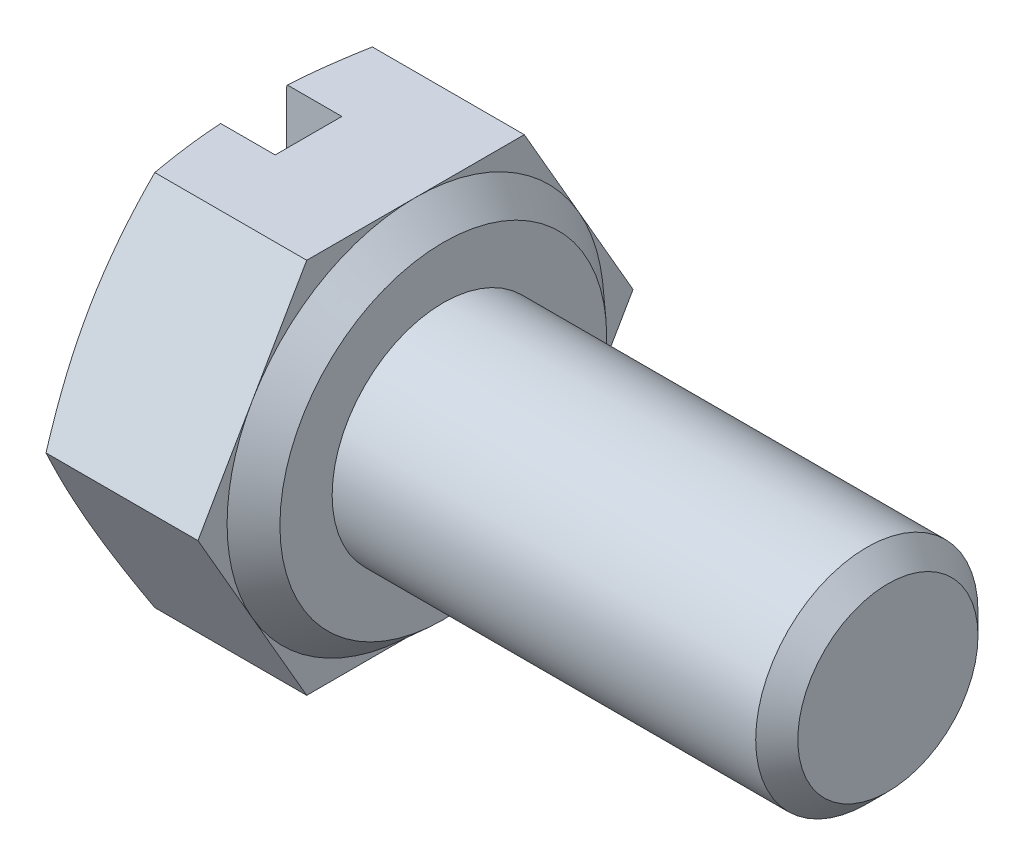
SolidWorks part; units mm, degrees
ref_plane "Front" through (0, 0, 0) normal (0, 0, 1) x (1, 0, 0)
ref_plane "Top" through (0, 0, 0) normal (0, 1, 0) x (1, 0, 0)
ref_plane "Right" through (0, 0, 0) normal (1, 0, 0) x (0, 0, -1)
sketch "Sketch-BaseHead" plane through (0, 0, 0) normal (1, 0, 0) x (0, 0, -1)
  line L1 (1.9572, -3.39) -> (3.9144, 0)
  line L2 (3.9144, 0) -> (1.9572, 3.39)
  line L3 (1.9572, 3.39) -> (-1.9572, 3.39)
  line L4 (-1.9572, 3.39) -> (-3.9144, 0)
  line L5 (-3.9144, 0) -> (-1.9572, -3.39)
  line L6 (-1.9572, -3.39) -> (1.9572, -3.39)
  circle A0 centre (0, 0) radius 3.39 construction
  dimension "s" = 6.78
extrude "BaseHead" add sketch "Sketch-BaseHead" along normal blind 2.925
ref_plane "Plane1" through (3.325, 0, 0) normal (1, 0, 0) x (0, 0, -1)
sketch "Sketch1" plane through (0, 0, 0) normal (0, 0, 1) x (1, 0, 0)
  line L0 (2.925, 0) -> (3.425, 0)
  line L1 (3.425, 0) -> (3.425, -2.94)
  line L2 (3.425, -2.94) -> (2.925, -3.39)
  line L3 (2.925, -3.39) -> (2.925, 0)
  dimension "D1" = 3.39
  dimension "D2" = 0.5
  dimension "D3" = 2.94
revolve "Revolve1" add sketch "Sketch1" angle 360 about axis through (-4.0016, 0, 0) along (1, 0, 0)
sketch "Sketch3" plane through (3.425, 0, 0) normal (1, 0, 0) x (0, 0, -1)
  circle A0 centre (0, 0) radius 2
  dimension "d" = 4
extrude "BaseBody" add sketch "Sketch3" along normal blind 8
cosmetic thread "ThreadCosmetic1" parameters "D2"=3.242
chamfer "Chamfer1" distance 0.379 angle 45 1 edges at (11.425, 0, -2)
fillet "HeadFillet" [suppressed] radius 0.2
sketch "Sketch4" plane through (-0.2646, 0, 5.9169) normal (0, 1, 0) x (0, 0, -1)
  line L0 (5.9169, 3.7369) -> (5.9169, -10.4477) construction
  line L2 (9.8313, -0.2646) -> (9.3069, -0.2646)
  line L4 (9.3069, -0.2646) -> (9.8313, -0.4555)
  line L6 (9.8313, -0.4555) -> (9.8313, -0.2646)
  dimension "D1" = 20
  dimension "D2" = 6.78
revolve "HeadChamfer" cut sketch "Sketch4" angle 360 about L0
sketch "Sketch5" plane through (0, 0, 0) normal (0, 1, 0) x (1, 0, 0)
  line L0 (0, 0.6) -> (0, -0.6)
  line L1 (1, -0.6) -> (1, 0.6)
  line L2 (1, 0.6) -> (0, 0.6)
  line L3 (0, -0.6) -> (1, -0.6)
  dimension "n" = 1.2
  dimension "t" = 1
extrude "Slot" cut sketch "Sketch5" against normal through all and the other way through all
sketch "Sketch6" plane through (0, 0, 0) normal (0, 0, 1) x (1, 0, 0)
  line L0 (3.425, 2.2) -> (3.804, 2.2)
  line L1 (3.804, 2.2) -> (3.804, 2)
  line L2 (3.804, 2) -> (3.6145, 1.6718)
  line L3 (3.425, 2) -> (3.6145, 1.6718)
  line L4 (3.425, 2.2) -> (3.425, 2)
  line L5 (14.0487, 0) -> (0, 0) construction
  line L6 (3.425, 2) -> (3.804, 2) construction
  line L7 (3.6145, 2) -> (3.6145, 1.6718) construction
  point P5 (3.6145, 2.2)
  dimension "D1" = 0.2
  dimension "D2" = 0.379
revolve "Cut-Revolve10" [suppressed] cut sketch "Sketch6" angle 360 about L5
pattern_linear "LPattern10" [suppressed] count 18 spacing 0.4548
equation "\"D1@Sketch1\" = \"s@Sketch-BaseHead\"/ 2 "
equation "\"D2@Sketch4\" = \"s@Sketch-BaseHead\""
equation "\"D1@Chamfer1\" =  ( \"d@Sketch3\" - \"D2@ThreadCosmetic1\" ) / 2 "
equation "\"D2@Sketch6\" = (  \"d@Sketch3\" - \"D2@ThreadCosmetic1\" )  / 2"
equation "\"D3@LPattern10\" = \"D2@Sketch6\" * 1.2"
equation "\"D1@LPattern10\" = \"l@BaseBody\" / \"D3@LPattern10\""
